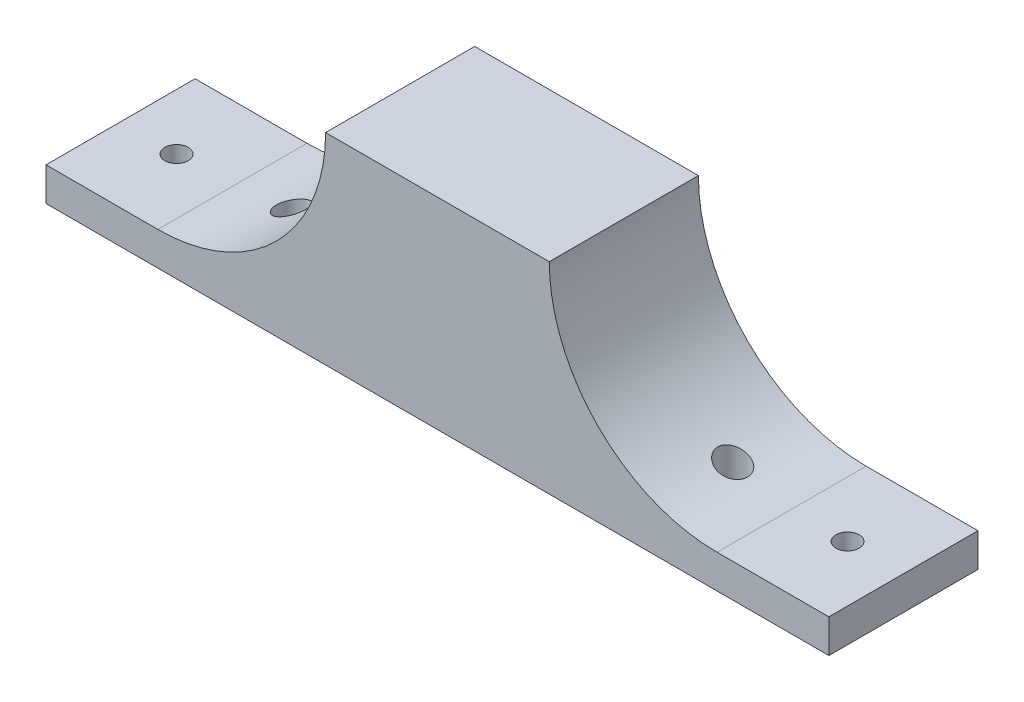
SolidWorks part; units mm, degrees
ref_plane "Front Plane" through (0, 0, 0) normal (0, 0, 1) x (1, 0, 0)
ref_plane "Top Plane" through (0, 0, 0) normal (0, 1, 0) x (1, 0, 0)
ref_plane "Right Plane" through (0, 0, 0) normal (1, 0, 0) x (0, 0, -1)
sketch "Sketch1" plane through (0, 0, 0) normal (0, 1, 0) x (1, 0, 0)
  line L1 (-60, 0) -> (0, 0)
  line L2 (-60, 0) -> (-60, -40)
  line L3 (-60, -40) -> (0, -40)
  line L4 (0, 0) -> (0, -40)
  dimension "D1" = 60
  dimension "D2" = 40
  dimension "D3" = 0
  dimension "D4" = 0
extrude "Boss-Extrude1" add sketch "Sketch1" along normal blind 54
sketch "Sketch2" plane through (0, 54, 0) normal (0, 1, 0) x (1, 0, 0)
  line L1 (-51.25, 11.25) -> (-8.75, 11.25)
  line L2 (-51.25, 11.25) -> (-51.25, -31.25)
  line L3 (-51.25, -31.25) -> (-8.75, -31.25)
  line L4 (-8.75, 11.25) -> (-8.75, -31.25)
  line L5 (-60, 0) -> (-60, -40) construction
  line L7 (-60, -40) -> (0, -40) construction
  line L9 (-43, -31.25) -> (-17, -31.25)
  line L10 (-43, -31.25) -> (-43, -40)
  line L11 (-43, -40) -> (-17, -40)
  line L12 (-17, -31.25) -> (-17, -40)
  point P4 (-51.25, -10)
  dimension "D1" = 42.5
  dimension "D2" = 42.5
  dimension "D3" = 8.75
  dimension "D4" = 8.75
  dimension "D5" = 26
  dimension "D6" = 0
  dimension "D7" = 8.25
  dimension "D8" = 0
sketch "Sketch3" plane through (0, 0, 0) normal (0, 1, 0) x (1, 0, 0)
  line L0 (0, -40) -> (0, 0) construction
  line L1 (0, 0) -> (75, 0)
  line L2 (0, 0) -> (0, -40)
  line L3 (0, -40) -> (75, -40)
  line L4 (75, 0) -> (75, -40)
  line L5 (0, 0) -> (-60, 0) construction
  circle A0 centre (29.2, -20) radius 4
  dimension "D5" = 20
  dimension "D7" = 8
  dimension "D1" = 0
  dimension "D2" = 0
  dimension "D3" = 40
  dimension "D4" = 75
  dimension "D6" = 45.8
extrude "Boss-Extrude2" add sketch "Sketch3" along normal blind 54
sketch "Sketch4" plane through (0, 0, 40) normal (0, 0, 1) x (1, 0, 0)
  line L0 (-60, 54) -> (75, 54) construction
  line L1 (75, 54) -> (75, 0) construction
  line L3 (45, 54) -> (75, 54)
  line L4 (45, 54) -> (45, 9)
  line L5 (45, 9) -> (75, 9)
  line L6 (75, 54) -> (75, 9)
  circle A0 centre (45, 54) radius 45
  line M7 (75, 0) -> (75, 54)
  line M8 (75, 54) -> (-60, 54)
  dimension "D3" = 90
  dimension "D1" = 0
  dimension "D2" = 30
  dimension "D4" = 0
  dimension "D5" = 30
  dimension "D6" = 0
  dimension "D7" = 45
extrude "Cut-Extrude2" cut sketch "Sketch4" against normal blind 60 contours A0 L5 M7 | A0 L4 M8 | L4 A0 L6 M8
ref_plane "Plane4" through (-30, 0, 0) normal (1, 0, 0) x (0, 0, -1)
hole_wizard "Tap Drill for M6 Helicoil1" positions "Sketch6" profile "Sketch7" hole size "M6x1.0" standard "ANSI Metric" end condition through all
sketch "Sketch6" plane through (0, 9, 0) normal (0, 1, 0) x (1, 0, 0)
  line L0 (45, 0) -> (75, 0) construction
  line L2 (75, 0) -> (75, -40) construction
  point P0 (60, -20)
  dimension "D1" = 20
  dimension "D2" = 15
sketch "Sketch7" plane through (60, 9, 20) normal (1, 0, 0) x (0, 0, 1)
  line L0 (0, 0) -> (0, 9)
  line L1 (0, 9) -> (3.125, 9)
  line L2 (3.125, 9) -> (3.125, 0)
  line L5 (3.125, 0) -> (0, 0)
  line L11 (0, -6.35) -> (0, 107.95) construction
  dimension "Thru Hole Dia." = 6.25
  dimension "Thru Hole Depth" = 9
mirror "Mirror1" about plane through (-30, 0, 0) normal (1, 0, 0) of "Tap Drill for M6 Helicoil1", "Cut-Extrude2", "Boss-Extrude2"
